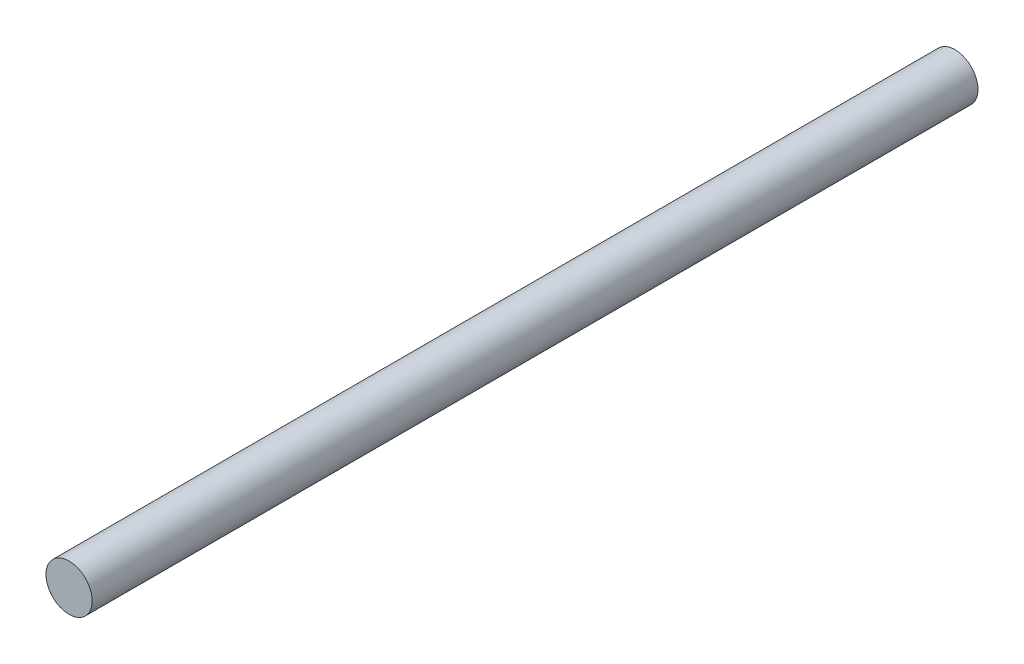
SolidWorks part; units mm, degrees
ref_plane "Front Plane" through (0, 0, 0) normal (0, 0, 1) x (1, 0, 0)
ref_plane "Top Plane" through (0, 0, 0) normal (0, 1, 0) x (1, 0, 0)
ref_plane "Right Plane" through (0, 0, 0) normal (1, 0, 0) x (0, 0, -1)
sketch "Sketch1" plane through (0, 0, 0) normal (0, 0, 1) x (1, 0, 0)
  circle A0 centre (0, 0) radius 0.5
extrude "Boss-Extrude1" add sketch "Sketch1" along normal blind 19.17
